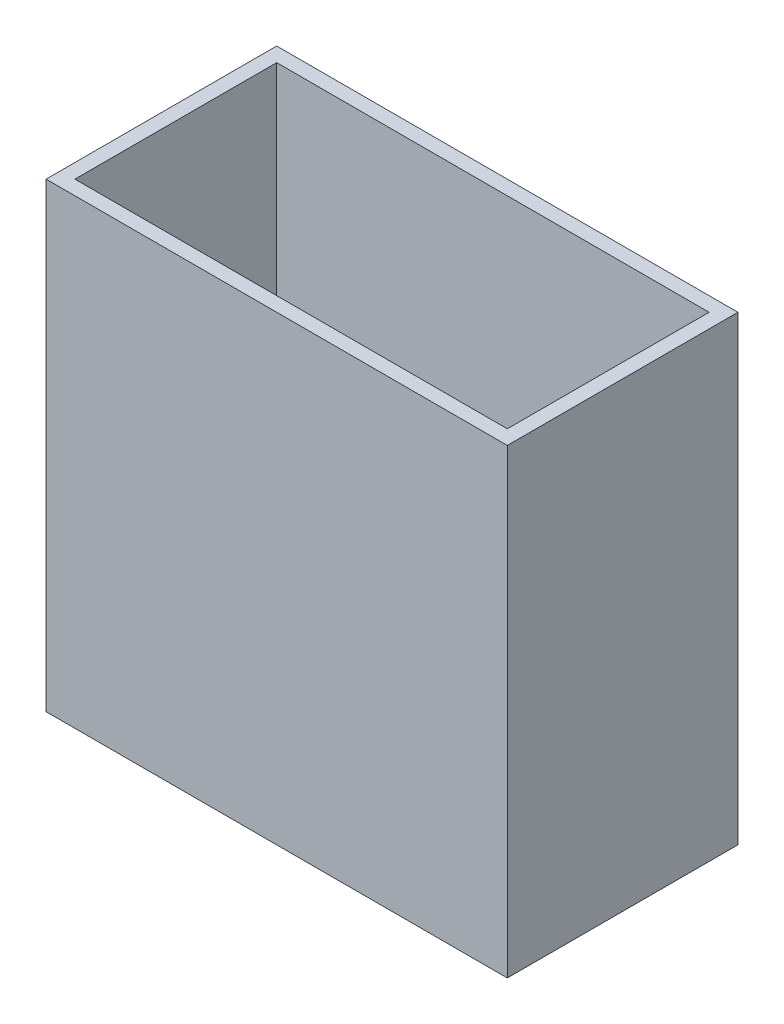
SolidWorks part; units mm, degrees
ref_plane "Front Plane" through (0, 0, 0) normal (0, 0, 1) x (1, 0, 0)
ref_plane "Top Plane" through (0, 0, 0) normal (0, 1, 0) x (1, 0, 0)
ref_plane "Right Plane" through (0, 0, 0) normal (1, 0, 0) x (0, 0, -1)
sketch "Sketch1" plane through (0, 0, 0) normal (0, 1, 0) x (1, 0, 0)
  line L1 (-26.5883, 11.6602) -> (24.2117, 11.6602)
  line L2 (-26.5883, 11.6602) -> (-26.5883, -13.7398)
  line L3 (-26.5883, -13.7398) -> (24.2117, -13.7398)
  line L4 (24.2117, 11.6602) -> (24.2117, -13.7398)
  line L5 (-25.0008, 10.0727) -> (22.6242, 10.0727)
  line L6 (-25.0008, 10.0727) -> (-25.0008, -12.1523)
  line L7 (-25.0008, -12.1523) -> (22.6242, -12.1523)
  line L8 (22.6242, 10.0727) -> (22.6242, -12.1523)
  dimension "D1" = 50.8
  dimension "D2" = 25.4
  dimension "D3" = 1.5875
  dimension "D4" = 1.5875
  dimension "D5" = 1.5875
  dimension "D6" = 1.5875
extrude "Boss-Extrude1" add sketch "Sketch1" along normal blind 50.8
